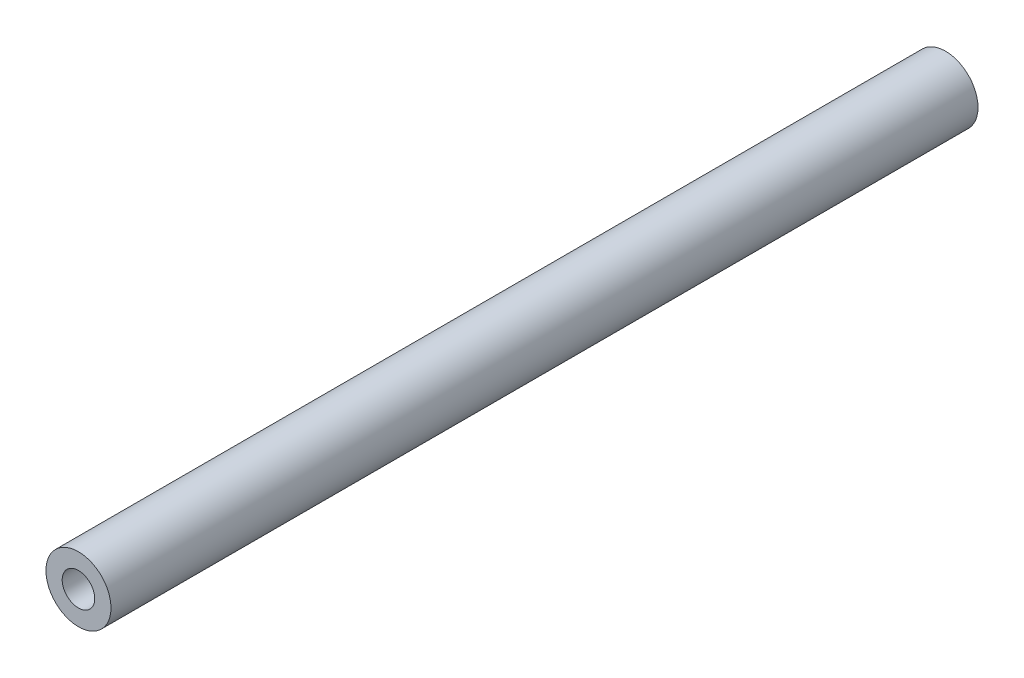
SolidWorks part; units mm, degrees
ref_plane "前视基准面" through (0, 0, 0) normal (0, 0, 1) x (1, 0, 0)
ref_plane "上视基准面" through (0, 0, 0) normal (0, 1, 0) x (1, 0, 0)
ref_plane "右视基准面" through (0, 0, 0) normal (1, 0, 0) x (0, 0, -1)
sketch "草图1" plane through (0, 0, 0) normal (0, 0, 1) x (1, 0, 0)
  circle A0 centre (0, 0) radius 3
  circle A1 centre (0, 0) radius 1.5
  dimension "D1" = 6
  dimension "D2" = 3
extrude "凸台-拉伸1" add sketch "草图1" along normal blind 80
